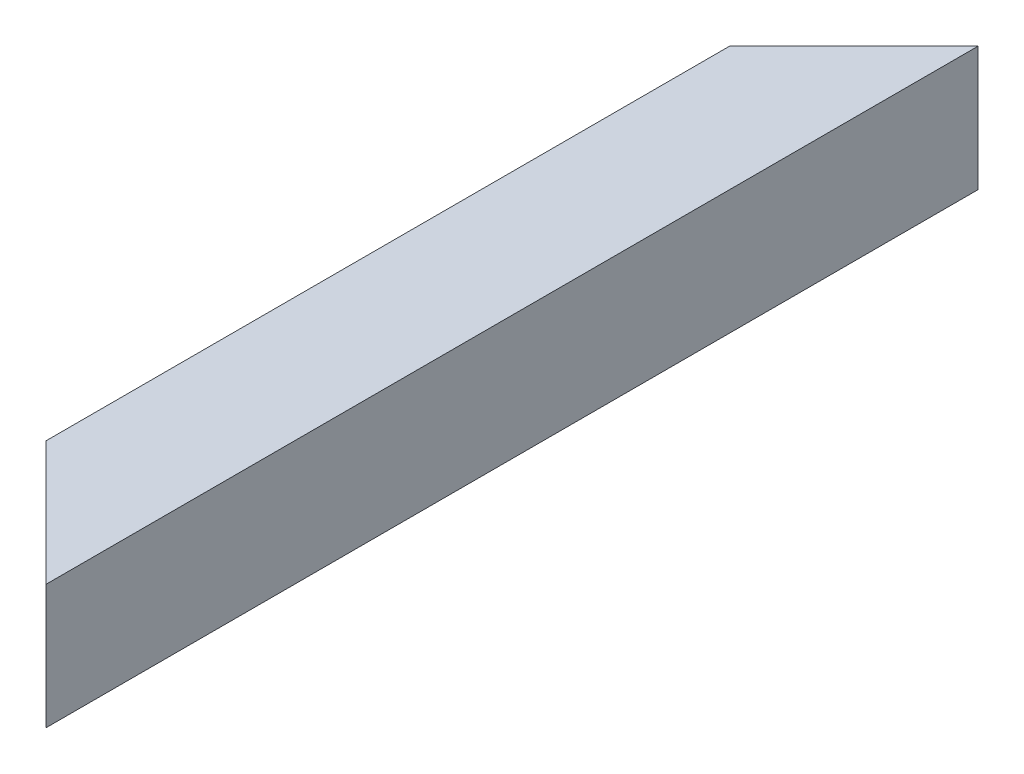
SolidWorks part; units mm, degrees
material "1.0037 (S235JR)"
ref_plane "Front Plane" through (0, 0, 0) normal (0, 0, 1) x (1, 0, 0)
ref_plane "Top Plane" through (0, 0, 0) normal (0, 1, 0) x (1, 0, 0)
ref_plane "Right Plane" through (0, 0, 0) normal (1, 0, 0) x (0, 0, -1)
curve "Curve1"
  spline degree 1 poles (0, 0, 0) (0, 0, 300) knots 0 0 1 1
sketch "Sketch1" plane through (0, 0, 0) normal (0, 0, 1) x (1, 0, 0)
  line L0 (0, 35.3535) -> (0, -33.8384) construction
  line L1 (-20, 20) -> (20, 20)
  line L2 (-20, 20) -> (-20, -20)
  line L3 (-20, -20) -> (20, -20)
  line L4 (20, 20) -> (20, -20)
  line L5 (-16, 16) -> (16, 16)
  line L6 (-16, 16) -> (-16, -16)
  line L7 (-16, -16) -> (16, -16)
  line L8 (16, 16) -> (16, -16)
  line L9 (-39.3939, 0) -> (41.5152, 0) construction
  dimension "D1" = 40
  dimension "D2" = 32
sweep "Sweep1" add profiles "Sketch1" path "Curve1"
sketch "Sketch2" plane through (0, 20, 0) normal (0, 1, 0) x (1, 0, 0)
  line L0 (20, 0) -> (-20, -40)
  line L1 (-20, 0) -> (-20, -300) construction
  line L2 (-20, -40) -> (-20, 0)
  line L3 (-20, 0) -> (20, 0)
  line L4 (20, -300) -> (-20, -260)
  line L5 (-20, -260) -> (-20, -300)
  line L6 (-20, -300) -> (20, -300)
  dimension "D1" = 45
  dimension "D2" = 45
extrude "Cut-Extrude1" cut sketch "Sketch2" against normal through all
